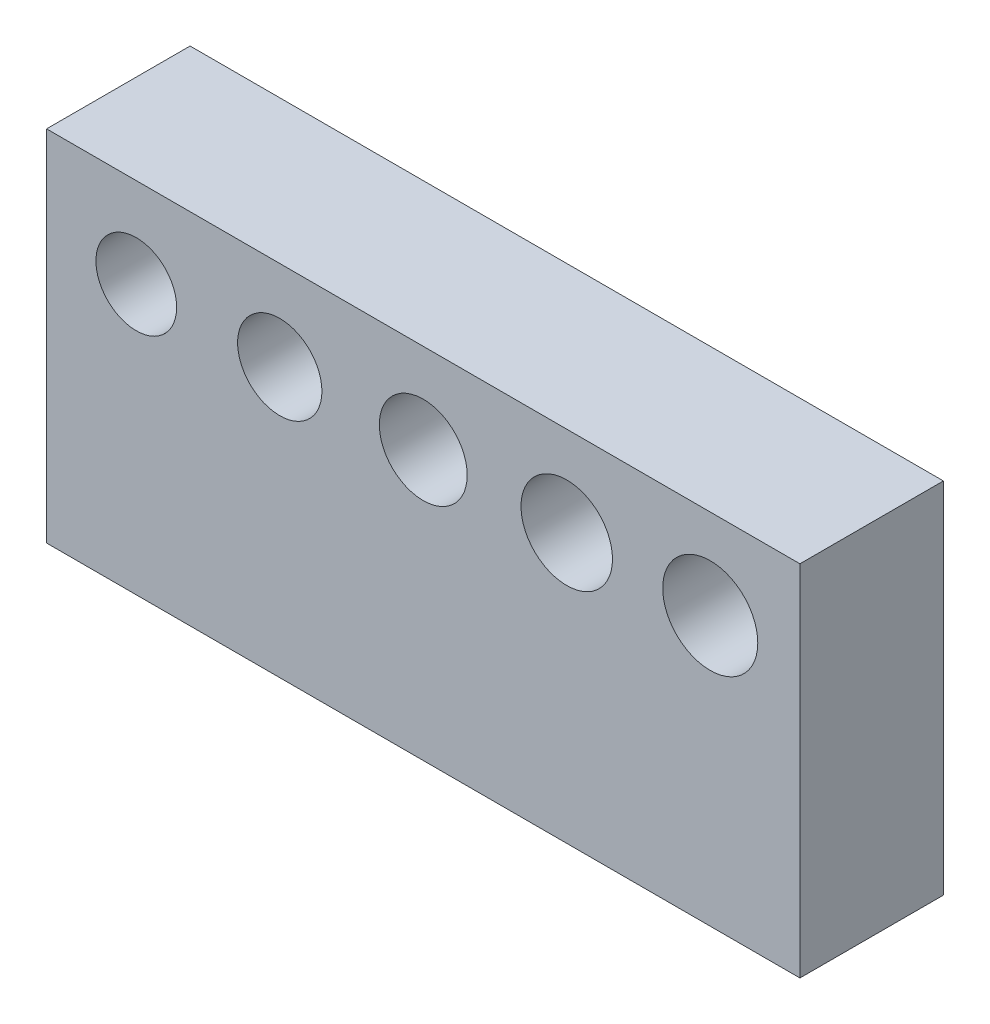
SolidWorks part; units mm, degrees
ref_plane "正面(Front)" through (0, 0, 0) normal (0, 0, 1) x (1, 0, 0)
ref_plane "平面(Top)" through (0, 0, 0) normal (0, 1, 0) x (1, 0, 0)
ref_plane "右側面(Right)" through (0, 0, 0) normal (1, 0, 0) x (0, 0, -1)
sketch "ｽｹｯﾁ1" plane through (0, 0, 0) normal (0, 0, 1) x (1, 0, 0)
  line L1 (-21, 10) -> (21, 10)
  line L2 (-21, 10) -> (-21, -10)
  line L3 (-21, -10) -> (21, -10)
  line L4 (21, 10) -> (21, -10)
  line L5 (-21, 10) -> (21, -10) construction
  line L6 (-21, -10) -> (21, 10) construction
  point P0 (0, 0)
  dimension "D1" = 42
  dimension "D2" = 20
extrude "ﾎﾞｽ - 押し出し1" add sketch "ｽｹｯﾁ1" along normal blind 8
sketch "ｽｹｯﾁ2" plane through (0, 0, 8) normal (0, 0, 1) x (1, 0, 0)
  line L0 (21, 10) -> (-21, 10) construction
  line L1 (-21, 10) -> (-21, -10) construction
  circle A0 centre (-16, 5) radius 2.25
  circle A1 centre (-8, 5) radius 2.35
  circle A2 centre (0, 5) radius 2.45
  circle A3 centre (8, 5) radius 2.55
  circle A4 centre (16, 5) radius 2.65
  point P6 (0, 0)
  dimension "D1" = 4.5
  dimension "D2" = 4.7
  dimension "D3" = 4.9
  dimension "D4" = 5.1
  dimension "D5" = 5
  dimension "D6" = 5
  dimension "D7" = 8
  dimension "D8" = 8
  dimension "D9" = 8
  dimension "D10" = 5.3
  dimension "D11" = 8
extrude "ｶｯﾄ - 押し出し1" cut sketch "ｽｹｯﾁ2" against normal through all
sketch "ｽｹｯﾁ3" plane through (0, -10, 0) normal (0, -1, 0) x (1, 0, 0)
  line L0 (-21, 8) -> (-21, 0) construction
  circle A0 centre (-16, 4) radius 2.15
  circle A1 centre (-8, 4) radius 2.25
  circle A2 centre (0, 4) radius 2.35
  circle A3 centre (8, 4) radius 2.45
  point P8 (0, 0)
  point P11 (-21, 4)
  dimension "D1" = 4.3
  dimension "D2" = 4.5
  dimension "D3" = 4.7
  dimension "D4" = 4.9
  dimension "D5" = 5
  dimension "D6" = 8
  dimension "D7" = 8
  dimension "D8" = 8
extrude "ｶｯﾄ - 押し出し2" cut sketch "ｽｹｯﾁ3" against normal blind 10
